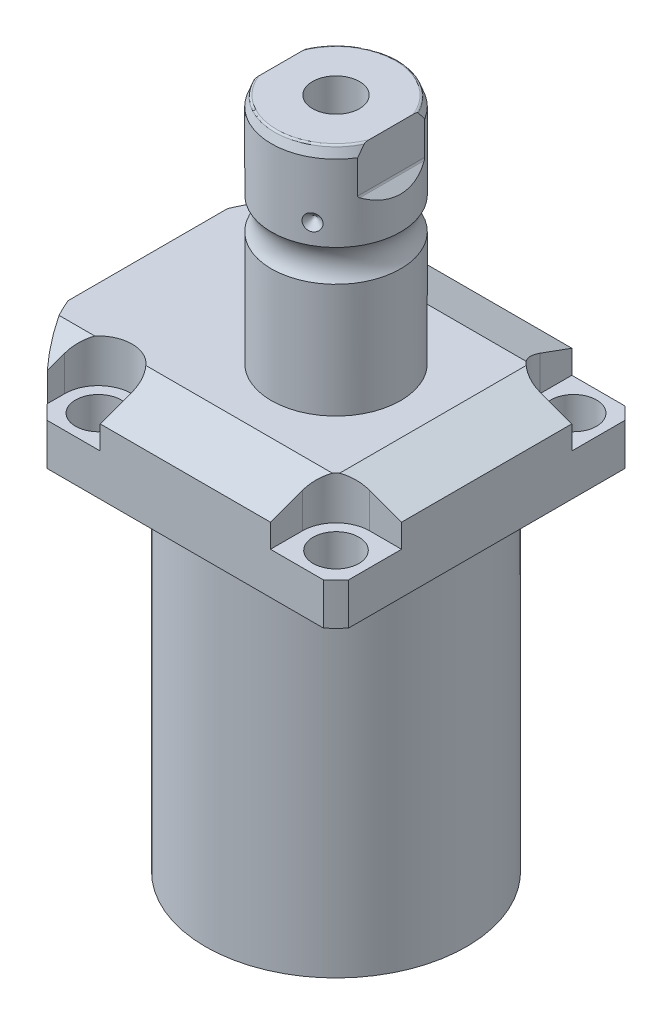
SolidWorks part; units mm, degrees
material "Alloy Steel"
ref_plane "Front Plane" through (0, 0, 0) normal (0, 0, 1) x (1, 0, 0)
ref_plane "Top Plane" through (0, 0, 0) normal (0, 1, 0) x (1, 0, 0)
ref_plane "Right Plane" through (0, 0, 0) normal (1, 0, 0) x (0, 0, -1)
ref_plane "Plane1" through (0, 0, 0) normal (0, 1, 0) x (0, 0, 1)
sketch "Sketch1" plane through (0, 0, 0) normal (0, 1, 0) x (0, 0, 1)
  line L0 (-44.45, 44.45) -> (44.45, 44.45)
  line L1 (44.45, 44.45) -> (44.45, -55.5498)
  line L2 (44.45, -55.5498) -> (-44.45, -55.5498)
  line L3 (-44.45, -55.5498) -> (-44.45, 44.45)
  line L4 (0, 0) -> (0, -60.6467) construction
  dimension "D1" = 55.5498
  dimension "D2" = 99.9998
  dimension "D3" = 88.9
extrude "Extrude1" add sketch "Sketch1" along normal blind 129.794
sketch "Sketch2" plane through (0, 0, 0) normal (0, -1, 0) x (1, 0, 0)
  circle A0 centre (0, 0) radius 60.325
  dimension "D1" = 120.65
extrude "Cut-Extrude1" cut sketch "Sketch2" against normal through all flip side to cut
ref_plane "Plane2" through (0, 0, 0) normal (1, 0, 0) x (0, 0, 1)
sketch "Sketch3" plane through (0, 0, 0) normal (1, 0, 0) x (0, 0, 1)
  line L0 (38.4937, 0) -> (38.4937, -104.775)
  line L1 (38.4937, -104.775) -> (76.5937, -104.775)
  line L2 (76.5937, -104.775) -> (76.5937, 0)
  line L3 (76.5937, 0) -> (38.4937, 0)
  line L4 (0, -93.345) -> (0, 4.445) construction
  line L5 (40.7836, 0) -> (-40.7836, 0) construction
  dimension "D1" = 76.9874
  dimension "D2" = 153.1874
  dimension "D3" = 104.775
revolve "Cut-Revolve1" cut sketch "Sketch3" angle 360 about L4
fillet "Fillet1" radius 0.381 1 edges at (0, 104.775, 38.4937)
sketch "Sketch4" plane through (0, 129.794, 0) normal (0, 1, 0) x (-1, 0, 0)
  line L0 (-44.45, 40.7836) -> (-44.45, -40.7836) construction
  line L1 (40.7836, 44.45) -> (-40.7836, 44.45) construction
  line L2 (-25.1206, -44.45) -> (-25.1206, -35.052)
  line L3 (-44.45, -44.45) -> (-25.1206, -44.45)
  line L4 (-44.45, -25.1206) -> (-44.45, -44.45)
  line L5 (-35.052, -25.1206) -> (-44.45, -25.1206)
  line L6 (44.9834, -44.45) -> (25.1206, -44.45)
  line L7 (25.1206, 44.45) -> (25.1206, 35.052)
  line L8 (44.9834, 44.45) -> (44.9834, 35.052)
  line L9 (44.9834, 44.45) -> (25.1206, 44.45)
  line L10 (-35.052, 25.1206) -> (-44.45, 25.1206)
  line L11 (-44.45, 25.1206) -> (-44.45, 44.45)
  line L12 (-44.45, 44.45) -> (-25.1206, 44.45)
  line L13 (-25.1206, 44.45) -> (-25.1206, 35.052)
  line L14 (-48.9217, 0) -> (49.4551, 0) construction
  line L15 (44.9834, -44.45) -> (44.9834, -35.052)
  line L16 (25.1206, -44.45) -> (25.1206, -35.052)
  arc A0 (25.1206, -35.052) -> (44.9834, -35.052) centre (35.052, -35.052) cw
  arc A1 (-35.052, -25.1206) -> (-25.1206, -35.052) centre (-35.052, -35.052) cw
  arc A2 (-35.052, 25.1206) -> (-25.1206, 35.052) centre (-35.052, 35.052) ccw
  arc A3 (25.1206, 35.052) -> (44.9834, 35.052) centre (35.052, 35.052) ccw
  dimension "D2" = 9.9314
  dimension "D1" = 35.052
  dimension "D3" = 35.052
  dimension "D4" = 35.052
extrude "Cut-Extrude2" cut sketch "Sketch4" against normal blind 12.7
ref_plane "Plane3" through (0, 0, 0) normal (1, 0, 0) x (0, 0, -1)
sketch "Sketch5" plane through (0, 0, 0) normal (1, 0, 0) x (0, 0, -1)
  line L0 (-28.575, 129.794) -> (-44.45, 124.016)
  line L1 (0, 0) -> (0, 154.1081) construction
  line L2 (-28.575, 129.794) -> (-44.45, 129.794)
  line L3 (-44.45, 129.794) -> (-44.45, 124.016)
  dimension "D1" = 15.875
  dimension "D2" = 20
extrude "Cut-Extrude9" cut sketch "Sketch5" against normal through all and the other way through all
mirror "Mirror1" about plane through (0, 0, 0) normal (0, 0, 1) of "Cut-Extrude9"
ref_plane "Plane7" through (0, 0, 0) normal (0, 0, 1) x (1, 0, 0)
sketch "Sketch9" plane through (0, 0, 0) normal (0, 0, 1) x (1, 0, 0)
  line L0 (28.575, 129.794) -> (44.45, 124.016)
  line L1 (44.45, 124.016) -> (44.45, 129.794)
  line L2 (44.45, 129.794) -> (28.575, 129.794)
  dimension "D1" = 15.875
  dimension "D2" = 20
extrude "Cut-Extrude7" cut sketch "Sketch9" against normal through all and the other way through all
ref_plane "Plane8" through (-41.402, 88.9, -18.1102) normal (1, 0, 0) x (0, 1, 0)
sketch "Sketch20" plane through (-41.402, 88.9, -18.1102) normal (1, 0, 0) x (0, 1, 0)
  line L0 (-88.9, 18.1102) -> (39.8401, 18.1102) construction
  line L1 (-7.2797, 36.2204) -> (36.9042, 36.2204) construction
  line L2 (15.875, 41.9227) -> (17.3228, 41.9227)
  line L3 (15.875, 58.8938) -> (15.875, -22.6734) construction
  line L4 (17.3228, 41.9227) -> (17.3228, 39.4716)
  line L5 (17.3228, 39.4716) -> (18.3388, 39.4716)
  line L6 (18.3388, 39.4716) -> (18.3388, 37.465)
  line L7 (18.3388, 37.465) -> (29.3116, 37.465)
  line L8 (29.3116, 37.465) -> (29.3116, 36.2204)
  line L9 (29.3116, 36.2204) -> (15.875, 36.2204)
  line L10 (15.875, 41.9227) -> (15.875, 36.2204)
  dimension "D1" = 18.1102
  dimension "D2" = 11.4046
  dimension "D3" = 1.4478
  dimension "D4" = 6.5024
  dimension "D5" = 1.016
  dimension "D6" = 2.4892
  dimension "D7" = 10.9728
revolve "Cut-Revolve4" cut sketch "Sketch20" angle 360 about L1
mirror "Mirror10" about plane through (0, 0, 0) normal (0, 0, 1) of "Cut-Revolve4"
sketch "Sketch10" plane through (-41.402, 88.9, -18.1102) normal (1, 0, 0) x (0, 1, 0)
  line L0 (-1.0325, 0) -> (1.5659, 0) construction
  line L1 (29.3116, 1.2446) -> (18.3388, 1.2446) construction
  line L2 (18.3388, -1.2446) -> (29.3116, -1.2446) construction
  line L3 (15.875, 58.8938) -> (15.875, -22.6734) construction
  circle A0 centre (16.1417, 4.5212) radius 1.1811
  dimension "D1" = 2.3622
  dimension "D2" = 0.2667
  dimension "D3" = 9.0424
revolve "Revolve4" add sketch "Sketch10" angle 360 about L0
ref_plane "Plane9" through (-41.402, 88.9, 18.1102) normal (1, 0, 0) x (0, 1, 0)
sketch "Sketch11" plane through (-41.402, 88.9, 18.1102) normal (1, 0, 0) x (0, 1, 0)
  line L0 (-1.0325, 0) -> (1.5659, 0) construction
  line L1 (29.3116, 1.2446) -> (18.3388, 1.2446) construction
  line L3 (15.875, 22.6734) -> (15.875, -58.8938) construction
  line L4 (18.3388, -1.2446) -> (29.3116, -1.2446) construction
  circle A0 centre (16.1417, 4.5212) radius 1.1811
  point P10 (0, 0)
  dimension "D1" = 2.3622
  dimension "D2" = 9.0424
  dimension "D3" = 0.2667
revolve "Revolve2" add sketch "Sketch11" angle 360 about L0
ref_plane "Plane10" through (-55.5498, 101.9048, 12.9794) normal (0, 0, 1) x (0, 1, 0)
sketch "S2D0007" plane through (-55.5498, 101.9048, 12.9794) normal (0, 0, 1) x (0, 1, 0)
  line L0 (15.875, 0) -> (26.3525, 0)
  line L1 (26.3525, 0) -> (26.3525, -0.254)
  line L2 (26.3525, -0.254) -> (22.0599, -0.254)
  line L3 (22.0599, -0.254) -> (21.5173, -2.8067)
  line L4 (21.5173, -2.8067) -> (20.8534, -3.4706)
  line L5 (20.8534, -3.4706) -> (20.8534, -14.224)
  line L6 (20.8534, -14.224) -> (15.875, -14.224)
  line L7 (15.875, -14.224) -> (15.875, 0)
  line L8 (15.875, -14.9352) -> (15.875, 0.7112) construction
  line L9 (2.8702, 0) -> (2.8702, -14.7662) construction
  line L10 (27.8892, 0) -> (2.8702, 0) construction
  dimension "D1" = 0.254
  dimension "D2" = 13.0048
  dimension "D3" = 12
  dimension "D4" = 0.254
  dimension "D5" = 20.955
  dimension "D6" = 12.3698
  dimension "D7" = 45
  dimension "D8" = 3.2166
  dimension "D9" = 9.9568
  dimension "D10" = 13.97
revolve "Cut-Revolve2" cut sketch "S2D0007" angle 360 about L8
pattern_linear "LPattern1" count 2 spacing 25.9588 along (0, 0, -1) of "Cut-Revolve2"
ref_plane "Plane12" through (0, 0, 0) normal (1, 0, 0) x (0, -1, 0)
sketch "Sketch15" plane through (0, 0, 0) normal (1, 0, 0) x (0, -1, 0)
  line L0 (-129.794, 0) -> (-129.794, 19.05)
  line L1 (-129.794, 19.05) -> (-163.4663, 19.05)
  line L2 (-172.8805, 19.05) -> (-195.4276, 19.05)
  line L3 (-198.3486, 17.9868) -> (-198.3486, 0)
  line L4 (-198.3486, 0) -> (-129.794, 0)
  line L5 (-197.6361, 0) -> (-64.6704, 0) construction
  line L6 (-129.794, 27.5233) -> (-129.794, -27.5233) construction
  line L7 (-104.775, 40.7836) -> (-104.775, 44.45) construction
  line L8 (-198.3486, 17.9868) -> (-195.4276, 19.05)
  arc A0 (-172.8805, 19.05) -> (-163.4663, 19.05) centre (-168.1734, 25.4254) ccw
  dimension "D2" = 20
  dimension "D4" = 7.9248
  dimension "D6" = 35.0012
  dimension "D1" = 93.5736
  dimension "D3" = 38.1
  dimension "D5" = 30.1752
  dimension "D7" = 2.921
revolve "Revolve3" add sketch "Sketch15" angle 360 about L5
ref_plane "Plane13" through (0, 0, 0) normal (0, 0, -1) x (0, -1, 0)
sketch "Sketch16" plane through (0, 0, 0) normal (0, 0, -1) x (0, -1, 0)
  line L0 (-198.3486, 19.05) -> (-182.5644, 19.05)
  line L1 (-198.3486, -19.05) -> (-198.3486, -16.2814)
  line L2 (-198.3486, 16.2814) -> (-185.6486, 16.2814)
  line L3 (-185.1098, 16.5046) -> (-182.5644, 19.05)
  line L4 (-185.1098, -16.5046) -> (-182.5644, -19.05)
  line L5 (-198.3486, -16.2814) -> (-185.6486, -16.2814)
  line L6 (-198.3486, 19.05) -> (-198.3486, 16.2814)
  line L7 (-198.3486, -19.05) -> (-182.5644, -19.05)
  line L8 (-194.0458, 0) -> (-125.0021, 0) construction
  line L11 (-198.3486, 17.9868) -> (-198.3486, -17.9868) construction
  line L12 (-172.8805, 19.05) -> (-195.4276, 19.05) construction
  arc A0 (-185.6486, 16.2814) -> (-185.1098, 16.5046) centre (-185.6486, 17.0434) ccw
  arc A1 (-185.6486, -16.2814) -> (-185.1098, -16.5046) centre (-185.6486, -17.0434) cw
  point P3 (-185.333, 16.2814)
  dimension "D4" = 0.762
  dimension "D1" = 32.5628
  dimension "D2" = 45
  dimension "D3" = 12.7
extrude "Cut-Extrude8" cut sketch "Sketch16" against normal mid plane 106.68
hole_wizard "Hole1" positions "Sketch18" profile "Sketch17" legacy end condition up to next
sketch "Sketch18" plane through (0, 117.094, 0) normal (0, 1, 0) x (-1, 0, 0)
  arc A0 (44.9834, -35.052) -> (25.1206, -35.052) centre (35.052, -35.052) ccw construction
  arc A1 (25.1206, 35.052) -> (44.9834, 35.052) centre (35.052, 35.052) ccw construction
  arc A2 (-35.052, 25.1206) -> (-25.1206, 35.052) centre (-35.052, 35.052) ccw construction
  arc A3 (-25.1206, -35.052) -> (-35.052, -25.1206) centre (-35.052, -35.052) ccw construction
  point P0 (-35.052, -35.052)
  point P1 (-35.052, 35.052)
  point P3 (35.052, 35.052)
  point P5 (35.052, -35.052)
sketch "Sketch17" plane through (35.052, 117.094, -35.052) normal (1, 0, 0) x (0, 0, 1)
  line L0 (0, 0) -> (0, 12.319)
  line L1 (0, 12.319) -> (6.7437, 12.319)
  line L2 (6.7437, 12.319) -> (6.7437, 0)
  line L3 (6.7437, 0) -> (0, 0)
  line L4 (0, 110) -> (0, -10) construction
  dimension "Diameter" = 13.4874
  dimension "Depth" = 12.319
chamfer "Chamfer1" distance 0.635 angle 45 2 edges at (-41.402, 107.2388, 16.8656) (-41.402, 107.2388, -16.8656)
sketch "Sketch21" plane through (0, 0, 0) normal (0, 0, 1) x (1, 0, 0)
  line L0 (0, 0) -> (0, 194.0957) construction
  line L1 (0, 172.9486) -> (6.9342, 177.1151)
  line L2 (6.9342, 177.1151) -> (6.9342, 198.3486)
  line L4 (6.9342, 198.3486) -> (0, 198.3486)
  line L5 (0, 198.3486) -> (0, 172.9486)
  line L6 (16.2814, 198.3486) -> (-16.2814, 198.3486) construction
  dimension "D1" = 13.8684
  dimension "D2" = 59
  dimension "D3" = 25.4
revolve "Cut-Revolve5" cut sketch "Sketch21" angle 360 about L0
fillet "Fillet2" radius 0.635 2 edges at (0, 198.3486, 17.9868) (0, 198.3486, -17.9868)
sketch "Sketch22" plane through (0, 0, 0) normal (0, 0, 1) x (1, 0, 0)
  line L0 (-37.9974, 178.8414) -> (37.12, 178.8414) construction
  line L1 (-19.05, 181.2544) -> (-16.637, 178.8414)
  line L2 (-16.637, 178.8414) -> (-19.05, 178.8414)
  line L3 (-19.05, 178.8414) -> (-19.05, 181.2544)
  line L4 (-19.05, 182.5644) -> (-19.05, 172.8805) construction
  arc A0 (-19.05, 163.4663) -> (-19.05, 172.8805) centre (-25.4254, 168.1734) ccw construction
  dimension "D2" = 10.668
  dimension "D1" = 4.826
  dimension "D3" = 45
revolve "Cut-Revolve6" cut sketch "Sketch22" angle 360 about L0
pattern_circular "CirPattern1" count 3 over 360 about axis through (0, 197.6361, 0) along (0, 1, 0) of "Cut-Revolve6"
